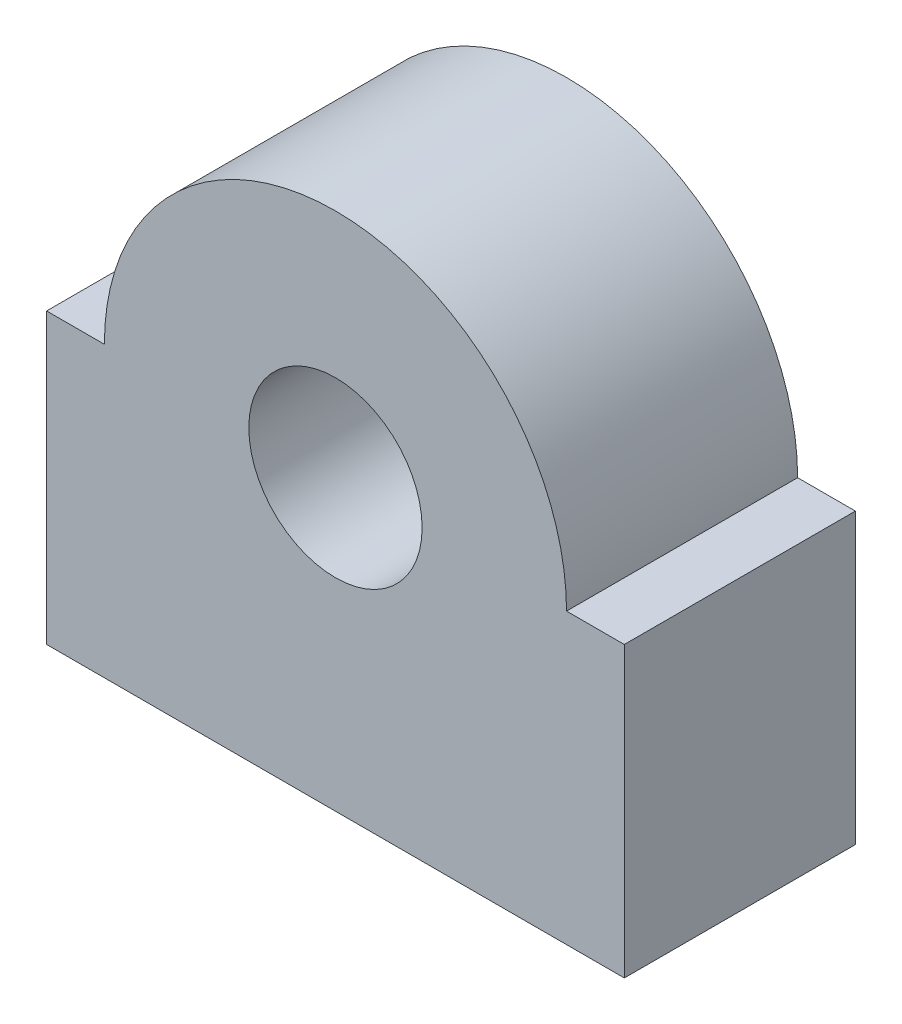
SolidWorks part; units mm, degrees
ref_plane "Front Plane" through (0, 0, 0) normal (0, 0, 1) x (1, 0, 0)
ref_plane "Top Plane" through (0, 0, 0) normal (0, 1, 0) x (1, 0, 0)
ref_plane "Right Plane" through (0, 0, 0) normal (1, 0, 0) x (0, 0, -1)
sketch "Sketch1" plane through (0, 0, 0) normal (0, 0, 1) x (1, 0, 0)
  line L0 (0, 100.2096) -> (0, -45.9815) construction
  line L1 (-63.5, 0) -> (63.5, 0)
  line L2 (-63.5, 0) -> (-63.5, 63.5)
  line L3 (-63.5, 63.5) -> (-50.8, 63.5)
  line L4 (63.5, 0) -> (63.5, 63.5)
  line L5 (50.8, 63.5) -> (63.5, 63.5)
  line L6 (-82.2487, 0) -> (93.1128, 0) construction
  arc A0 (-50.8, 63.5) -> (50.8, 63.5) centre (0, 63.5) cw
  circle A1 centre (0, 63.5) radius 19.05
  dimension "D3" = 50.8
  dimension "D4" = 38.1
  dimension "D1" = 63.5
  dimension "D2" = 127
extrude "Boss-Extrude1" add sketch "Sketch1" along normal blind 50.8
